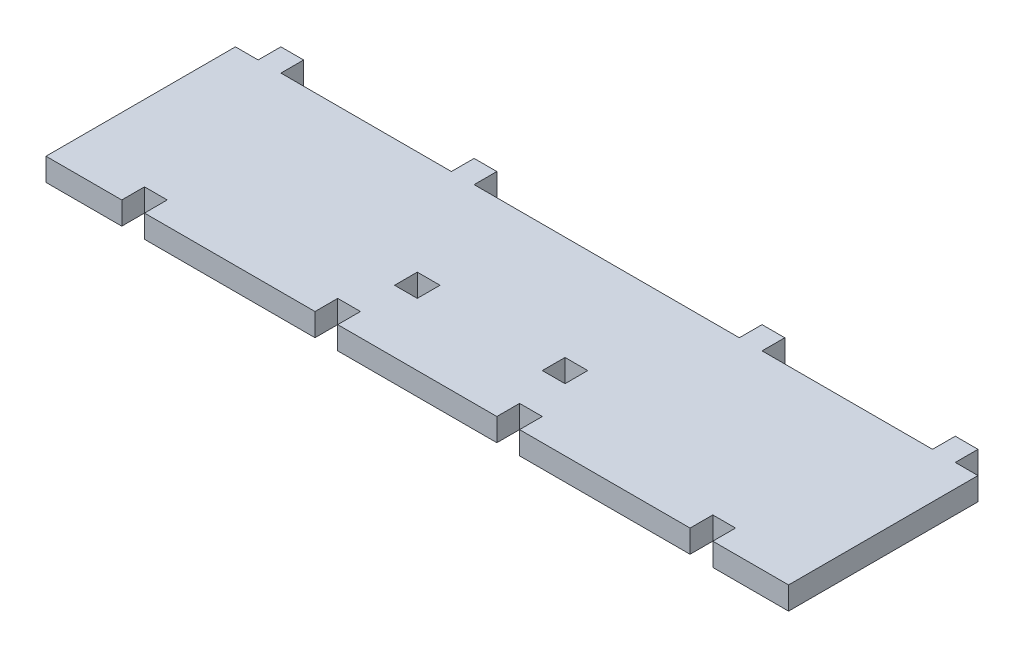
SolidWorks part; units mm, degrees
material "Pine"
ref_plane "정면" through (0, 0, 0) normal (0, 0, 1) x (1, 0, 0)
ref_plane "윗면" through (0, 0, 0) normal (0, 1, 0) x (1, 0, 0)
ref_plane "우측면" through (0, 0, 0) normal (1, 0, 0) x (0, 0, -1)
sketch "Sketch1" plane through (0, 0, 0) normal (0, 0, 1) x (1, 0, 0)
  line L0 (0, -55.5594) -> (0, 89.4924) construction
  line L1 (98, 0) -> (-98, 0)
  line L2 (-98, 0) -> (-98, 6)
  line L3 (-98, 6) -> (98, 6)
  line L4 (98, 0) -> (98, 6)
  point P8 (0, 6)
  point P9 (0, 0)
  dimension "D1" = 98
  dimension "D2" = 6
extrude "Boss-Extrude1" add sketch "Sketch1" along normal blind 50
sketch "Sketch2" plane through (0, 0, 0) normal (0, 0, -1) x (-1, 0, 0)
  line L0 (0, -28.0858) -> (0, 36.535) construction
  line L1 (98, 0) -> (-98, 0) construction
  line L2 (-92, 0) -> (-92, 6)
  line L3 (-98, 6) -> (98, 6) construction
  line L4 (-92, 6) -> (-86, 6)
  line L5 (-86, 6) -> (-86, 0)
  line L6 (-86, 0) -> (-92, 0)
  line L7 (-98, 0) -> (-98, 6) construction
  line L8 (-41, 0) -> (-41, 6)
  line L9 (-41, 6) -> (-35, 6)
  line L10 (-35, 6) -> (-35, 0)
  line L11 (-35, 0) -> (-41, 0)
  line L12 (35, 0) -> (41, 0)
  line L13 (35, 6) -> (35, 0)
  line L14 (41, 6) -> (35, 6)
  line L15 (41, 0) -> (41, 6)
  line L16 (86, 0) -> (92, 0)
  line L17 (86, 6) -> (86, 0)
  line L18 (92, 6) -> (86, 6)
  line L19 (92, 0) -> (92, 6)
  point P17 (-38, 6)
  dimension "D1" = 6
  dimension "D2" = 6
  dimension "D3" = 6
  dimension "D4" = 6
  dimension "D5" = 6
  dimension "D6" = 45
  dimension "D7" = 6
extrude "Boss-Extrude2" add sketch "Sketch2" along normal blind 6
sketch "Sketch3" plane through (0, 6, 0) normal (0, 1, 0) x (1, 0, 0)
  line L0 (0, 40.6529) -> (0, -78.0081) construction
  line L1 (78, -50) -> (78, -44)
  line L2 (78, -44) -> (72, -44)
  line L3 (72, -44) -> (72, -50)
  line L4 (72, -50) -> (78, -50)
  line L5 (98, -50) -> (98, 0) construction
  line L6 (98, -50) -> (-98, -50) construction
  line L7 (27, -50) -> (27, -44)
  line L8 (27, -44) -> (21, -44)
  line L9 (21, -44) -> (21, -50)
  line L10 (21, -50) -> (27, -50)
  line L11 (-21, -50) -> (-27, -50)
  line L12 (-21, -44) -> (-21, -50)
  line L13 (-27, -44) -> (-21, -44)
  line L14 (-27, -50) -> (-27, -44)
  line L15 (-72, -50) -> (-78, -50)
  line L16 (-72, -44) -> (-72, -50)
  line L17 (-78, -44) -> (-72, -44)
  line L18 (-78, -50) -> (-78, -44)
  dimension "D1" = 6
  dimension "D2" = 6
  dimension "D3" = 20
  dimension "D4" = 45
  dimension "D5" = 6
  dimension "D6" = 6
extrude "Cut-Extrude1" cut sketch "Sketch3" against normal blind 6
sketch "Sketch4" plane through (0, 6, 0) normal (0, 1, 0) x (1, 0, 0)
  line L0 (0, 50.3189) -> (0, -101.6218) construction
sketch "Sketch5" plane through (0, 0, 0) normal (0, -1, 0) x (1, 0, 0)
  line L0 (0, 77.6053) -> (0, -23.3108) construction
  line L1 (0, -50.3189) -> (0, 101.6218) construction
  line L2 (-22.5, 27.5) -> (-16.5, 27.5)
  line L3 (-16.5, 27.5) -> (-16.5, 33.5)
  line L4 (-16.5, 33.5) -> (-22.5, 33.5)
  line L5 (-22.5, 33.5) -> (-22.5, 27.5)
  line L6 (-21, 44) -> (-27, 44) construction
  line L7 (22.5, 33.5) -> (22.5, 27.5)
  line L8 (16.5, 33.5) -> (22.5, 33.5)
  line L9 (16.5, 27.5) -> (16.5, 33.5)
  line L10 (22.5, 27.5) -> (16.5, 27.5)
  dimension "D1" = 6
  dimension "D2" = 6
  dimension "D3" = 16.5
  dimension "D4" = 10.5
extrude "Cut-Extrude2" cut sketch "Sketch5" against normal blind 6
